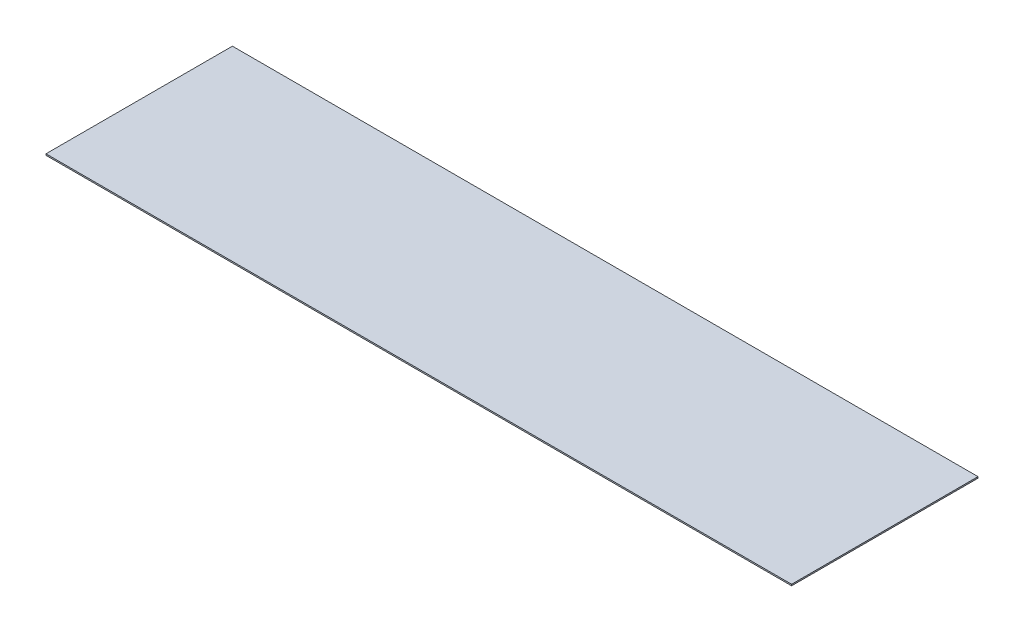
SolidWorks part; units mm, degrees
ref_plane "Front Plane" through (0, 0, 0) normal (0, 0, 1) x (1, 0, 0)
ref_plane "Top Plane" through (0, 0, 0) normal (0, 1, 0) x (1, 0, 0)
ref_plane "Right Plane" through (0, 0, 0) normal (1, 0, 0) x (0, 0, -1)
sketch "Sketch1" plane through (0, 0, 0) normal (0, 1, 0) x (1, 0, 0)
  line L1 (40, -10) -> (-40, -10)
  line L2 (40, -10) -> (40, 10)
  line L3 (40, 10) -> (-40, 10)
  line L4 (-40, -10) -> (-40, 10)
  line L5 (40, -10) -> (-40, 10) construction
  line L6 (40, 10) -> (-40, -10) construction
  point P0 (0, 0)
  dimension "D1" = 80
  dimension "D2" = 20
extrude "Boss-Extrude1" add sketch "Sketch1" along normal blind 0.15
